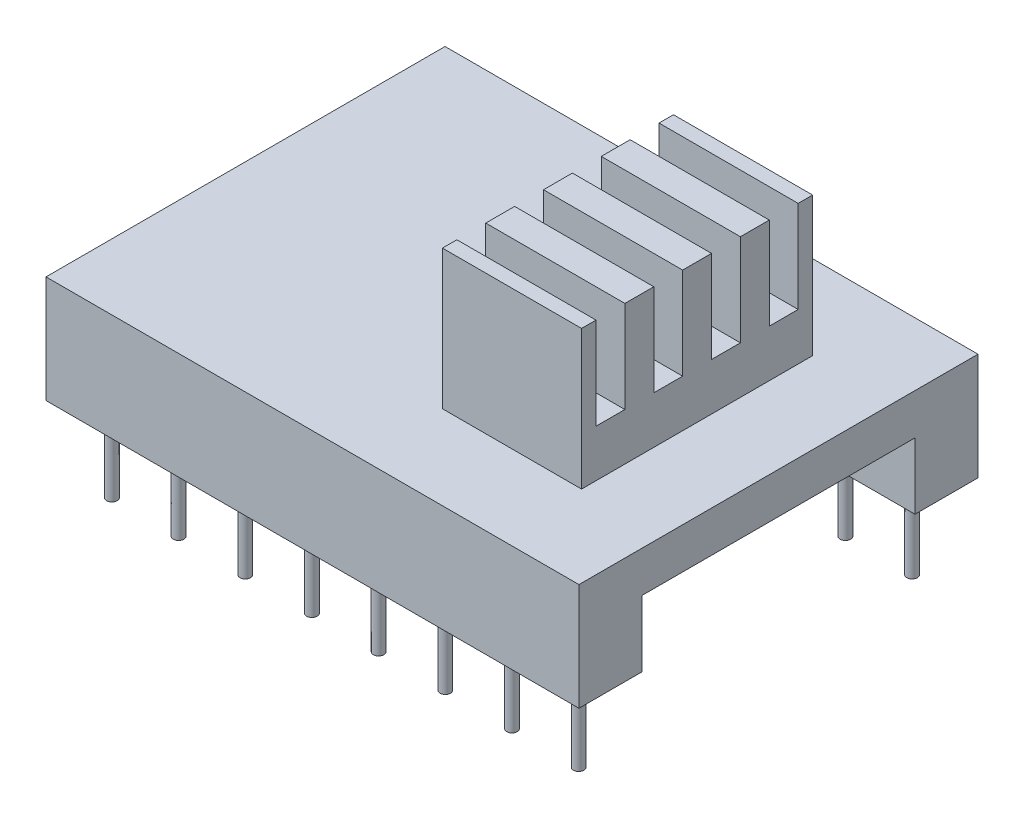
SolidWorks part; units mm, degrees
ref_plane "Front Plane" through (0, 0, 0) normal (0, 0, 1) x (1, 0, 0)
ref_plane "Top Plane" through (0, 0, 0) normal (0, 1, 0) x (1, 0, 0)
ref_plane "Right Plane" through (0, 0, 0) normal (1, 0, 0) x (0, 0, -1)
sketch "Sketch1" plane through (0, 0, 0) normal (0, 1, 0) x (1, 0, 0)
  line L1 (10.15, 7.6) -> (-10.15, 7.6)
  line L2 (10.15, 7.6) -> (10.15, -7.6)
  line L3 (10.15, -7.6) -> (-10.15, -7.6)
  line L4 (-10.15, 7.6) -> (-10.15, -7.6)
  line L5 (10.15, 7.6) -> (-10.15, -7.6) construction
  line L6 (10.15, -7.6) -> (-10.15, 7.6) construction
  point P0 (0, 0)
  dimension "D1" = 20.3
  dimension "D2" = 15.2
extrude "Boss-Extrude1" add sketch "Sketch1" along normal blind 1.56
sketch "Sketch2" plane through (0, 0, 0) normal (0, -1, 0) x (1, 0, 0)
  line L0 (10.15, 7.6) -> (10.15, -7.6) construction
  line L1 (-10.15, 7.6) -> (10.15, 7.6)
  line L2 (-10.15, 7.6) -> (-10.15, 5.2)
  line L3 (-10.15, 5.2) -> (10.15, 5.2)
  line L4 (10.15, 7.6) -> (10.15, 5.2)
  line L6 (-10.15, -7.6) -> (10.15, -7.6)
  line L7 (-10.15, -7.6) -> (-10.15, -5.2)
  line L8 (-10.15, -5.2) -> (10.15, -5.2)
  line L9 (10.15, -7.6) -> (10.15, -5.2)
  dimension "D1" = 2.4
  dimension "D2" = 2.4
extrude "Boss-Extrude2" add sketch "Sketch2" along normal blind 2.52
sketch "Sketch3" plane through (0, -2.52, 0) normal (0, -1, 0) x (1, 0, 0)
  line L0 (-10.15, 7.6) -> (-10.15, 5.2) construction
  circle A0 centre (-8.89, 6.35) radius 0.2
  point P3 (0, 0)
  dimension "D1" = 0.4
  dimension "D2" = 1.26
  dimension "D3" = 6.35
extrude "Boss-Extrude3" add sketch "Sketch3" along normal blind 3.2 contours A0
pattern_linear "LPattern1" count 8 spacing 2.54 along (1, 0, 0) of "Boss-Extrude3"
mirror "Mirror1" about plane through (0, 0, 0) normal (0, 0, 1) of "LPattern1", "Boss-Extrude3"
sketch "Sketch4" plane through (0, 1.56, 0) normal (0, 1, 0) x (1, 0, 0)
  line L1 (1.75, 4.4) -> (7.05, 4.4)
  line L2 (1.75, 4.4) -> (1.75, -4.4)
  line L3 (1.75, -4.4) -> (7.05, -4.4)
  line L4 (7.05, 4.4) -> (7.05, -4.4)
  line L5 (1.75, 4.4) -> (7.05, -4.4) construction
  line L6 (1.75, -4.4) -> (7.05, 4.4) construction
  point P0 (4.4, 0)
  dimension "D1" = 8.8
  dimension "D2" = 5.3
  dimension "D3" = 4.4
extrude "Boss-Extrude4" add sketch "Sketch4" along normal blind 5.3
sketch "Sketch5" plane through (7.05, 0, 0) normal (1, 0, 0) x (0, 0, -1)
  line L0 (-4.4, 6.86) -> (4.4, 6.86) construction
  line L1 (-3.85, 6.86) -> (-2.75, 6.86)
  line L2 (-3.85, 6.86) -> (-3.85, 3.36)
  line L3 (-3.85, 3.36) -> (-2.75, 3.36)
  line L4 (-2.75, 6.86) -> (-2.75, 3.36)
  line L5 (-4.4, 1.56) -> (4.4, 1.56) construction
  line L6 (-1.65, 6.86) -> (-0.55, 6.86)
  line L7 (-1.65, 6.86) -> (-1.65, 3.36)
  line L8 (-1.65, 3.36) -> (-0.55, 3.36)
  line L9 (-0.55, 6.86) -> (-0.55, 3.36)
  line L10 (0.55, 6.86) -> (1.65, 6.86)
  line L11 (0.55, 6.86) -> (0.55, 3.36)
  line L12 (0.55, 3.36) -> (1.65, 3.36)
  line L13 (1.65, 6.86) -> (1.65, 3.36)
  line L14 (2.75, 6.86) -> (3.85, 6.86)
  line L15 (2.75, 6.86) -> (2.75, 3.36)
  line L16 (2.75, 3.36) -> (3.85, 3.36)
  line L17 (3.85, 6.86) -> (3.85, 3.36)
  dimension "D1" = 1.8
  dimension "D2" = 1.1
  dimension "D3" = 1.1
  dimension "D4" = 1.1
  dimension "D5" = 1.1
  dimension "D6" = 0.55
extrude "Cut-Extrude1" cut sketch "Sketch5" against normal blind 5.3
equation "\"D2@Sketch2\"=\"D1@Sketch2\""
equation "\"D2@Sketch5\"=8.8/8"
equation "\"D3@Sketch5\"=\"D2@Sketch5\""
equation "\"D4@Sketch5\"=\"D3@Sketch5\""
equation "\"D5@Sketch5\"=\"D4@Sketch5\""
equation "\"D6@Sketch5\"=\"D2@Sketch5\"/2"
